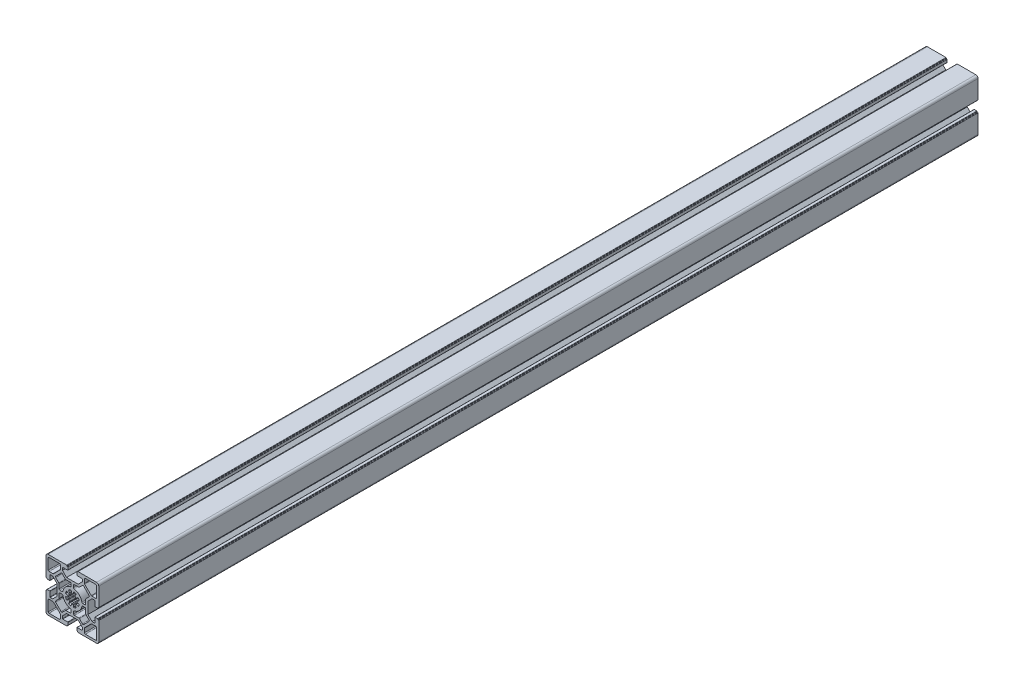
SolidWorks part; units mm, degrees
material "6063 T5"
ref_plane "Спереди" through (0, 0, 0) normal (0, 0, 1) x (1, 0, 0)
ref_plane "Сверху" through (0, 0, 0) normal (0, 1, 0) x (1, 0, 0)
ref_plane "Справа" through (0, 0, 0) normal (1, 0, 0) x (0, 0, -1)
sketch "Эскиз1" plane through (0, 0, 0) normal (0, 0, 1) x (1, 0, 0)
  line L0 (-22.505, 28.5436) -> (22.495, 28.5436) construction
  line L1 (-22.454, 23.9579) -> (22.546, 23.9579) construction
  line L73 (-30.0123, 36.8991) -> (29.9877, 36.8991) construction
  line L127 (-30, 11.25) -> (-30, 27.5)
  line L128 (-27.5, 30) -> (-11.25, 30)
  line L129 (11.25, 30) -> (27.5, 30)
  line L130 (30, 27.5) -> (30, 11.25)
  line L131 (-30, -11.25) -> (-30, -27.5)
  line L132 (-27.5, -30) -> (-11.25, -30)
  line L133 (11.25, -30) -> (27.5, -30)
  line L134 (30, -27.5) -> (30, -11.25)
  line L135 (-21.4071, 13.9929) -> (-13.9929, 21.4071)
  line L136 (-26.5, 27.5) -> (-14.7, 27.5)
  line L137 (-27.5, 26.5) -> (-27.5, 14.7)
  line L138 (-26.5, 13.7) -> (-22.1142, 13.7)
  line L139 (-13.7, 26.5) -> (-13.7, 22.1142)
  line L140 (0, 0) -> (-15.9071, 15.9071) construction
  line L141 (-12.8665, 18.9477) -> (-18.9477, 12.8665)
  line L142 (-18.9477, 11.4523) -> (-15.4929, 7.9976)
  line L143 (-15.2, 7.2905) -> (-15.2, 2.3)
  line L144 (-14.2, 1.3) -> (-11.7775, 1.3)
  line L145 (-1.3, 14.2) -> (-1.3, 11.7775)
  line L146 (-7.2905, 15.2) -> (-2.3, 15.2)
  line L147 (-11.4523, 18.9477) -> (-7.9976, 15.4929)
  line L148 (15.2, 7.2905) -> (15.2, 2.3)
  line L149 (14.2, 1.3) -> (11.7775, 1.3)
  line L150 (1.3, 14.2) -> (1.3, 11.7775)
  line L151 (7.2905, 15.2) -> (2.3, 15.2)
  line L152 (11.4523, 18.9477) -> (7.9976, 15.4929)
  line L153 (18.9477, 12.8665) -> (12.8665, 18.9477)
  line L154 (18.9477, 11.4523) -> (15.4929, 7.9976)
  line L155 (7.2905, -15.2) -> (2.3, -15.2)
  line L156 (1.3, -14.2) -> (1.3, -11.7775)
  line L157 (14.2, -1.3) -> (11.7775, -1.3)
  line L158 (15.2, -7.2905) -> (15.2, -2.3)
  line L159 (18.9477, -11.4523) -> (15.4929, -7.9976)
  line L160 (12.8665, -18.9477) -> (18.9477, -12.8665)
  line L161 (11.4523, -18.9477) -> (7.9976, -15.4929)
  line L162 (-15.2, -7.2905) -> (-15.2, -2.3)
  line L163 (-14.2, -1.3) -> (-11.7775, -1.3)
  line L164 (-1.3, -14.2) -> (-1.3, -11.7775)
  line L165 (-7.2905, -15.2) -> (-2.3, -15.2)
  line L166 (-11.4523, -18.9477) -> (-7.9976, -15.4929)
  line L167 (-18.9477, -12.8665) -> (-12.8665, -18.9477)
  line L168 (-18.9477, -11.4523) -> (-15.4929, -7.9976)
  line L169 (26.5, 13.7) -> (22.1142, 13.7)
  line L170 (13.9929, 21.4071) -> (21.4071, 13.9929)
  line L171 (13.7, 26.5) -> (13.7, 22.1142)
  line L172 (26.5, 27.5) -> (14.7, 27.5)
  line L173 (27.5, 26.5) -> (27.5, 14.7)
  line L174 (13.7, -26.5) -> (13.7, -22.1142)
  line L175 (21.4071, -13.9929) -> (13.9929, -21.4071)
  line L176 (26.5, -13.7) -> (22.1142, -13.7)
  line L177 (27.5, -26.5) -> (27.5, -14.7)
  line L178 (26.5, -27.5) -> (14.7, -27.5)
  line L179 (-26.5, -13.7) -> (-22.1142, -13.7)
  line L180 (-13.9929, -21.4071) -> (-21.4071, -13.9929)
  line L181 (-13.7, -26.5) -> (-13.7, -22.1142)
  line L182 (-26.5, -27.5) -> (-14.7, -27.5)
  line L183 (-27.5, -26.5) -> (-27.5, -14.7)
  arc A78 (-30, -27.5) -> (-27.5, -30) centre (-27.5, -27.5) ccw
  arc A79 (27.5, -30) -> (30, -27.5) centre (27.5, -27.5) ccw
  arc A80 (27.5, 30) -> (30, 27.5) centre (27.5, 27.5) cw
  arc A81 (-30, 27.5) -> (-27.5, 30) centre (-27.5, 27.5) cw
  arc A82 (-10.7961, 2.1083) -> (-2.1083, 10.7961) centre (0, 0) cw
  arc A83 (-11.7775, 1.3) -> (-10.7961, 2.1083) centre (-11.7775, 2.3) ccw
  arc A84 (-15.2, 2.3) -> (-14.2, 1.3) centre (-14.2, 2.3) ccw
  arc A85 (-15.4929, 7.9976) -> (-15.2, 7.2905) centre (-16.2, 7.2905) cw
  arc A86 (-18.9477, 12.8665) -> (-18.9477, 11.4523) centre (-18.2406, 12.1594) ccw
  arc A87 (-1.3, 11.7775) -> (-2.1083, 10.7961) centre (-2.3, 11.7775) cw
  arc A88 (-2.3, 15.2) -> (-1.3, 14.2) centre (-2.3, 14.2) cw
  arc A89 (-7.9976, 15.4929) -> (-7.2905, 15.2) centre (-7.2905, 16.2) ccw
  arc A90 (-12.8665, 18.9477) -> (-11.4523, 18.9477) centre (-12.1594, 18.2406) cw
  arc A91 (15.2, 2.3) -> (14.2, 1.3) centre (14.2, 2.3) cw
  arc A92 (11.7775, 1.3) -> (10.7961, 2.1083) centre (11.7775, 2.3) cw
  arc A93 (2.1083, 10.7961) -> (10.7961, 2.1083) centre (0, 0) cw
  arc A94 (1.3, 11.7775) -> (2.1083, 10.7961) centre (2.3, 11.7775) ccw
  arc A95 (2.3, 15.2) -> (1.3, 14.2) centre (2.3, 14.2) ccw
  arc A96 (7.9976, 15.4929) -> (7.2905, 15.2) centre (7.2905, 16.2) cw
  arc A97 (12.8665, 18.9477) -> (11.4523, 18.9477) centre (12.1594, 18.2406) ccw
  arc A98 (18.9477, 12.8665) -> (18.9477, 11.4523) centre (18.2406, 12.1594) cw
  arc A99 (15.4929, 7.9976) -> (15.2, 7.2905) centre (16.2, 7.2905) ccw
  arc A100 (2.3, -15.2) -> (1.3, -14.2) centre (2.3, -14.2) cw
  arc A101 (1.3, -11.7775) -> (2.1083, -10.7961) centre (2.3, -11.7775) cw
  arc A102 (10.7961, -2.1083) -> (2.1083, -10.7961) centre (0, 0) cw
  arc A103 (11.7775, -1.3) -> (10.7961, -2.1083) centre (11.7775, -2.3) ccw
  arc A104 (15.2, -2.3) -> (14.2, -1.3) centre (14.2, -2.3) ccw
  arc A105 (15.4929, -7.9976) -> (15.2, -7.2905) centre (16.2, -7.2905) cw
  arc A106 (18.9477, -12.8665) -> (18.9477, -11.4523) centre (18.2406, -12.1594) ccw
  arc A107 (12.8665, -18.9477) -> (11.4523, -18.9477) centre (12.1594, -18.2406) cw
  arc A108 (7.9976, -15.4929) -> (7.2905, -15.2) centre (7.2905, -16.2) ccw
  arc A109 (-15.2, -2.3) -> (-14.2, -1.3) centre (-14.2, -2.3) cw
  arc A110 (-11.7775, -1.3) -> (-10.7961, -2.1083) centre (-11.7775, -2.3) cw
  arc A111 (-2.1083, -10.7961) -> (-10.7961, -2.1083) centre (0, 0) cw
  arc A112 (-1.3, -11.7775) -> (-2.1083, -10.7961) centre (-2.3, -11.7775) ccw
  arc A113 (-2.3, -15.2) -> (-1.3, -14.2) centre (-2.3, -14.2) ccw
  arc A114 (-7.9976, -15.4929) -> (-7.2905, -15.2) centre (-7.2905, -16.2) cw
  arc A115 (-12.8665, -18.9477) -> (-11.4523, -18.9477) centre (-12.1594, -18.2406) ccw
  arc A116 (-18.9477, -12.8665) -> (-18.9477, -11.4523) centre (-18.2406, -12.1594) cw
  arc A117 (-15.4929, -7.9976) -> (-15.2, -7.2905) centre (-16.2, -7.2905) ccw
  arc A118 (-21.4071, 13.9929) -> (-22.1142, 13.7) centre (-22.1142, 14.7) cw
  arc A119 (-27.5, 14.7) -> (-26.5, 13.7) centre (-26.5, 14.7) ccw
  arc A120 (-13.9929, 21.4071) -> (-13.7, 22.1142) centre (-14.7, 22.1142) ccw
  arc A121 (-14.7, 27.5) -> (-13.7, 26.5) centre (-14.7, 26.5) cw
  arc A122 (-26.5, 27.5) -> (-27.5, 26.5) centre (-26.5, 26.5) ccw
  arc A123 (21.4071, 13.9929) -> (22.1142, 13.7) centre (22.1142, 14.7) ccw
  arc A124 (13.9929, 21.4071) -> (13.7, 22.1142) centre (14.7, 22.1142) cw
  arc A125 (14.7, 27.5) -> (13.7, 26.5) centre (14.7, 26.5) ccw
  arc A126 (27.5, 26.5) -> (26.5, 27.5) centre (26.5, 26.5) ccw
  arc A127 (27.5, 14.7) -> (26.5, 13.7) centre (26.5, 14.7) cw
  arc A128 (13.9929, -21.4071) -> (13.7, -22.1142) centre (14.7, -22.1142) ccw
  arc A129 (21.4071, -13.9929) -> (22.1142, -13.7) centre (22.1142, -14.7) cw
  arc A130 (27.5, -14.7) -> (26.5, -13.7) centre (26.5, -14.7) ccw
  arc A131 (26.5, -27.5) -> (27.5, -26.5) centre (26.5, -26.5) ccw
  arc A132 (14.7, -27.5) -> (13.7, -26.5) centre (14.7, -26.5) cw
  arc A133 (-21.4071, -13.9929) -> (-22.1142, -13.7) centre (-22.1142, -14.7) ccw
  arc A134 (-13.9929, -21.4071) -> (-13.7, -22.1142) centre (-14.7, -22.1142) cw
  arc A135 (-14.7, -27.5) -> (-13.7, -26.5) centre (-14.7, -26.5) ccw
  arc A136 (-27.5, -26.5) -> (-26.5, -27.5) centre (-26.5, -26.5) ccw
  arc A137 (-27.5, -14.7) -> (-26.5, -13.7) centre (-26.5, -14.7) cw
  point P3 (0, 0)
  point P6 (0, 0)
  point P28 (-15.2, 7.7047)
  point P31 (-19.6548, 12.1594)
  point P45 (-21.7, 13.7)
  point P60 (0, 0)
  point P121 (0, 0)
  point P124 (-27.5, 13.7)
  point P179 (0, 0)
  point P237 (0, 0)
  line B0 (-17.7, 0) -> (-30, 0) construction
  line B1 (-30, -6.1) -> (-30, 6.1) construction
  line B2 (-29.7, 6.1) -> (-29.3, 6.1)
  line B3 (-29, 5.8) -> (-29, 5.4)
  line B4 (-28.7, 5.1) -> (-25.8, 5.1)
  line B5 (-25.5, 5.4) -> (-25.5, 10.95)
  line B6 (-25.2, 11.25) -> (-22.35, 11.25)
  line B7 (-22.35, 11.25) -> (-17.7, 6.6)
  line B8 (-22.35, -11.25) -> (-17.7, -6.6)
  line B9 (-25.2, -11.25) -> (-22.35, -11.25)
  line B10 (-25.5, -5.4) -> (-25.5, -10.95)
  line B11 (-28.7, -5.1) -> (-25.8, -5.1)
  line B12 (-29, -5.8) -> (-29, -5.4)
  line B13 (-29.7, -6.1) -> (-29.3, -6.1)
  line B14 (-17.7, 6.6) -> (-17.7, -6.6)
  line B15 (-30, 6.4) -> (-30, 11.25)
  line B16 (-30, -6.4) -> (-30, -11.25)
  arc B17 (-25.2, -11.25) -> (-25.5, -10.95) centre (-25.2, -10.95) cw
  arc B18 (-25.5, -5.4) -> (-25.8, -5.1) centre (-25.8, -5.4) ccw
  arc B19 (-28.7, -5.1) -> (-29, -5.4) centre (-28.7, -5.4) ccw
  arc B20 (-29, -5.8) -> (-29.3, -6.1) centre (-29.3, -5.8) cw
  arc B21 (-29.7, -6.1) -> (-30, -6.4) centre (-29.7, -6.4) ccw
  arc B22 (-25.5, 10.95) -> (-25.2, 11.25) centre (-25.2, 10.95) cw
  arc B23 (-25.8, 5.1) -> (-25.5, 5.4) centre (-25.8, 5.4) ccw
  arc B24 (-29, 5.4) -> (-28.7, 5.1) centre (-28.7, 5.4) ccw
  arc B25 (-29.3, 6.1) -> (-29, 5.8) centre (-29.3, 5.8) cw
  arc B26 (-29.7, 6.1) -> (-30, 6.4) centre (-29.7, 6.4) cw
  line B27 (0, 17.7) -> (0, 30) construction
  line B28 (-6.1, 30) -> (6.1, 30) construction
  line B29 (6.1, 29.7) -> (6.1, 29.3)
  line B30 (5.8, 29) -> (5.4, 29)
  line B31 (5.1, 28.7) -> (5.1, 25.8)
  line B32 (5.4, 25.5) -> (10.95, 25.5)
  line B33 (11.25, 25.2) -> (11.25, 22.35)
  line B34 (11.25, 22.35) -> (6.6, 17.7)
  line B35 (-11.25, 22.35) -> (-6.6, 17.7)
  line B36 (-11.25, 25.2) -> (-11.25, 22.35)
  line B37 (-5.4, 25.5) -> (-10.95, 25.5)
  line B38 (-5.1, 28.7) -> (-5.1, 25.8)
  line B39 (-5.8, 29) -> (-5.4, 29)
  line B40 (-6.1, 29.7) -> (-6.1, 29.3)
  line B41 (6.6, 17.7) -> (-6.6, 17.7)
  line B42 (6.4, 30) -> (11.25, 30)
  line B43 (-6.4, 30) -> (-11.25, 30)
  arc B44 (-11.25, 25.2) -> (-10.95, 25.5) centre (-10.95, 25.2) cw
  arc B45 (-5.4, 25.5) -> (-5.1, 25.8) centre (-5.4, 25.8) ccw
  arc B46 (-5.1, 28.7) -> (-5.4, 29) centre (-5.4, 28.7) ccw
  arc B47 (-5.8, 29) -> (-6.1, 29.3) centre (-5.8, 29.3) cw
  arc B48 (-6.1, 29.7) -> (-6.4, 30) centre (-6.4, 29.7) ccw
  arc B49 (10.95, 25.5) -> (11.25, 25.2) centre (10.95, 25.2) cw
  arc B50 (5.1, 25.8) -> (5.4, 25.5) centre (5.4, 25.8) ccw
  arc B51 (5.4, 29) -> (5.1, 28.7) centre (5.4, 28.7) ccw
  arc B52 (6.1, 29.3) -> (5.8, 29) centre (5.8, 29.3) cw
  arc B53 (6.1, 29.7) -> (6.4, 30) centre (6.4, 29.7) cw
  line B54 (17.7, 0) -> (30, 0) construction
  line B55 (30, 6.1) -> (30, -6.1) construction
  line B56 (29.7, -6.1) -> (29.3, -6.1)
  line B57 (29, -5.8) -> (29, -5.4)
  line B58 (28.7, -5.1) -> (25.8, -5.1)
  line B59 (25.5, -5.4) -> (25.5, -10.95)
  line B60 (25.2, -11.25) -> (22.35, -11.25)
  line B61 (22.35, -11.25) -> (17.7, -6.6)
  line B62 (22.35, 11.25) -> (17.7, 6.6)
  line B63 (25.2, 11.25) -> (22.35, 11.25)
  line B64 (25.5, 5.4) -> (25.5, 10.95)
  line B65 (28.7, 5.1) -> (25.8, 5.1)
  line B66 (29, 5.8) -> (29, 5.4)
  line B67 (29.7, 6.1) -> (29.3, 6.1)
  line B68 (17.7, -6.6) -> (17.7, 6.6)
  line B69 (30, -6.4) -> (30, -11.25)
  line B70 (30, 6.4) -> (30, 11.25)
  arc B71 (25.2, 11.25) -> (25.5, 10.95) centre (25.2, 10.95) cw
  arc B72 (25.5, 5.4) -> (25.8, 5.1) centre (25.8, 5.4) ccw
  arc B73 (28.7, 5.1) -> (29, 5.4) centre (28.7, 5.4) ccw
  arc B74 (29, 5.8) -> (29.3, 6.1) centre (29.3, 5.8) cw
  arc B75 (29.7, 6.1) -> (30, 6.4) centre (29.7, 6.4) ccw
  arc B76 (25.5, -10.95) -> (25.2, -11.25) centre (25.2, -10.95) cw
  arc B77 (25.8, -5.1) -> (25.5, -5.4) centre (25.8, -5.4) ccw
  arc B78 (29, -5.4) -> (28.7, -5.1) centre (28.7, -5.4) ccw
  arc B79 (29.3, -6.1) -> (29, -5.8) centre (29.3, -5.8) cw
  arc B80 (29.7, -6.1) -> (30, -6.4) centre (29.7, -6.4) cw
  line B81 (0, -17.7) -> (0, -30) construction
  line B82 (6.1, -30) -> (-6.1, -30) construction
  line B83 (-6.1, -29.7) -> (-6.1, -29.3)
  line B84 (-5.8, -29) -> (-5.4, -29)
  line B85 (-5.1, -28.7) -> (-5.1, -25.8)
  line B86 (-5.4, -25.5) -> (-10.95, -25.5)
  line B87 (-11.25, -25.2) -> (-11.25, -22.35)
  line B88 (-11.25, -22.35) -> (-6.6, -17.7)
  line B89 (11.25, -22.35) -> (6.6, -17.7)
  line B90 (11.25, -25.2) -> (11.25, -22.35)
  line B91 (5.4, -25.5) -> (10.95, -25.5)
  line B92 (5.1, -28.7) -> (5.1, -25.8)
  line B93 (5.8, -29) -> (5.4, -29)
  line B94 (6.1, -29.7) -> (6.1, -29.3)
  line B95 (-6.6, -17.7) -> (6.6, -17.7)
  line B96 (-6.4, -30) -> (-11.25, -30)
  line B97 (6.4, -30) -> (11.25, -30)
  arc B98 (11.25, -25.2) -> (10.95, -25.5) centre (10.95, -25.2) cw
  arc B99 (5.4, -25.5) -> (5.1, -25.8) centre (5.4, -25.8) ccw
  arc B100 (5.1, -28.7) -> (5.4, -29) centre (5.4, -28.7) ccw
  arc B101 (5.8, -29) -> (6.1, -29.3) centre (5.8, -29.3) cw
  arc B102 (6.1, -29.7) -> (6.4, -30) centre (6.4, -29.7) ccw
  arc B103 (-10.95, -25.5) -> (-11.25, -25.2) centre (-10.95, -25.2) cw
  arc B104 (-5.1, -25.8) -> (-5.4, -25.5) centre (-5.4, -25.8) ccw
  arc B105 (-5.4, -29) -> (-5.1, -28.7) centre (-5.4, -28.7) ccw
  arc B106 (-6.1, -29.3) -> (-5.8, -29) centre (-5.8, -29.3) cw
  arc B107 (-6.1, -29.7) -> (-6.4, -30) centre (-6.4, -29.7) cw
  line B108 (0, 0) -> (3.6062, 3.6062) construction
  line B109 (1.3637, 7.358) -> (1.0164, 5.4842)
  line B110 (3.1592, 4.5967) -> (4.2386, 6.1672)
  line B111 (0, 0) -> (0, 5.1) construction
  arc B112 (0.478, -5.0776) -> (-0.478, -5.0776) centre (0, 0) cw
  arc B113 (-6.8804, -4.0816) -> (-7.7513, -1.979) centre (0, 0) cw
  arc B114 (3.9283, 3.2524) -> (3.2524, 3.9283) centre (0, 0) ccw
  arc B115 (4.0816, 6.8804) -> (1.979, 7.7513) centre (0, 0) ccw
  arc B116 (0.478, 5.0776) -> (-0.478, 5.0776) centre (0, 0) ccw
  line B117 (-1.3637, 7.358) -> (-1.0164, 5.4842)
  arc B118 (4.0816, -6.8804) -> (1.979, -7.7513) centre (0, 0) cw
  arc B119 (-3.9283, -3.2524) -> (-3.2524, -3.9283) centre (0, 0) ccw
  line B120 (-3.1592, -4.5967) -> (-4.2386, -6.1672)
  line B121 (0, 0) -> (6.3318, 0) construction
  line B122 (4.5967, 3.1592) -> (6.1672, 4.2386)
  line B123 (7.358, 1.3637) -> (5.4842, 1.0164)
  line B124 (-7.358, 1.3637) -> (-5.4842, 1.0164)
  line B125 (-4.5967, 3.1592) -> (-6.1672, 4.2386)
  line B126 (-3.1592, 4.5967) -> (-4.2386, 6.1672)
  line B127 (7.358, -1.3637) -> (5.4842, -1.0164)
  line B128 (4.5967, -3.1592) -> (6.1672, -4.2386)
  line B129 (3.1592, -4.5967) -> (4.2386, -6.1672)
  line B130 (1.3637, -7.358) -> (1.0164, -5.4842)
  line B131 (-1.3637, -7.358) -> (-1.0164, -5.4842)
  line B132 (-4.5967, -3.1592) -> (-6.1672, -4.2386)
  line B133 (-7.358, -1.3637) -> (-5.4842, -1.0164)
  arc B134 (5.0776, 0.478) -> (5.0776, -0.478) centre (0, 0) cw
  arc B135 (6.8804, 4.0816) -> (7.7513, 1.979) centre (0, 0) cw
  arc B136 (-5.0776, 0.478) -> (-5.0776, -0.478) centre (0, 0) ccw
  arc B137 (-6.8804, 4.0816) -> (-7.7513, 1.979) centre (0, 0) ccw
  arc B138 (-3.9283, 3.2524) -> (-3.2524, 3.9283) centre (0, 0) cw
  arc B139 (-4.0816, 6.8804) -> (-1.979, 7.7513) centre (0, 0) cw
  arc B140 (6.8804, -4.0816) -> (7.7513, -1.979) centre (0, 0) ccw
  arc B141 (3.9283, -3.2524) -> (3.2524, -3.9283) centre (0, 0) cw
  arc B142 (-4.0816, -6.8804) -> (-1.979, -7.7513) centre (0, 0) ccw
  arc B143 (-1.979, 7.7513) -> (-1.3637, 7.358) centre (-1.8554, 7.2669) cw
  arc B144 (-4.0816, 6.8804) -> (-4.2386, 6.1672) centre (-3.8265, 6.4504) ccw
  arc B145 (-3.2524, 3.9283) -> (-3.1592, 4.5967) centre (-3.5713, 4.3135) ccw
  arc B146 (-3.9283, 3.2524) -> (-4.5967, 3.1592) centre (-4.3135, 3.5713) cw
  arc B147 (-6.8804, 4.0816) -> (-6.1672, 4.2386) centre (-6.4504, 3.8265) cw
  arc B148 (-7.7513, 1.979) -> (-7.358, 1.3637) centre (-7.2669, 1.8554) ccw
  arc B149 (-5.0776, 0.478) -> (-5.4842, 1.0164) centre (-5.5754, 0.5248) ccw
  arc B150 (-5.4842, -1.0164) -> (-5.0776, -0.478) centre (-5.5754, -0.5248) ccw
  arc B151 (-7.7513, -1.979) -> (-7.358, -1.3637) centre (-7.2669, -1.8554) cw
  arc B152 (-6.8804, -4.0816) -> (-6.1672, -4.2386) centre (-6.4504, -3.8265) ccw
  arc B153 (-3.9283, -3.2524) -> (-4.5967, -3.1592) centre (-4.3135, -3.5713) ccw
  arc B154 (-3.2524, -3.9283) -> (-3.1592, -4.5967) centre (-3.5713, -4.3135) cw
  arc B155 (-4.0816, -6.8804) -> (-4.2386, -6.1672) centre (-3.8265, -6.4504) cw
  arc B156 (-1.979, -7.7513) -> (-1.3637, -7.358) centre (-1.8554, -7.2669) ccw
  arc B157 (-0.478, -5.0776) -> (-1.0164, -5.4842) centre (-0.5248, -5.5754) ccw
  arc B158 (0.478, -5.0776) -> (1.0164, -5.4842) centre (0.5248, -5.5754) cw
  arc B159 (1.979, -7.7513) -> (1.3637, -7.358) centre (1.8554, -7.2669) cw
  arc B160 (4.0816, -6.8804) -> (4.2386, -6.1672) centre (3.8265, -6.4504) ccw
  arc B161 (3.2524, -3.9283) -> (3.1592, -4.5967) centre (3.5713, -4.3135) ccw
  arc B162 (3.9283, -3.2524) -> (4.5967, -3.1592) centre (4.3135, -3.5713) cw
  arc B163 (6.8804, -4.0816) -> (6.1672, -4.2386) centre (6.4504, -3.8265) cw
  arc B164 (7.7513, -1.979) -> (7.358, -1.3637) centre (7.2669, -1.8554) ccw
  arc B165 (5.4842, -1.0164) -> (5.0776, -0.478) centre (5.5754, -0.5248) cw
  arc B166 (5.0776, 0.478) -> (5.4842, 1.0164) centre (5.5754, 0.5248) cw
  arc B167 (7.7513, 1.979) -> (7.358, 1.3637) centre (7.2669, 1.8554) cw
  arc B168 (6.8804, 4.0816) -> (6.1672, 4.2386) centre (6.4504, 3.8265) ccw
  arc B169 (4.5967, 3.1592) -> (3.9283, 3.2524) centre (4.3135, 3.5713) cw
  arc B170 (3.1592, 4.5967) -> (3.2524, 3.9283) centre (3.5713, 4.3135) ccw
  arc B171 (4.2386, 6.1672) -> (4.0816, 6.8804) centre (3.8265, 6.4504) ccw
  arc B172 (1.3637, 7.358) -> (1.979, 7.7513) centre (1.8554, 7.2669) cw
  arc B173 (-1.0164, 5.4842) -> (-0.478, 5.0776) centre (-0.5248, 5.5754) ccw
  arc B174 (1.0164, 5.4842) -> (0.478, 5.0776) centre (0.5248, 5.5754) cw
  dimension "D5" = 60
  dimension "D3" = 4
  dimension "D11" = 45
  dimension "D6" = 13.8
  dimension "D7" = 2.5
  dimension "D20" = 4
  dimension "D23" = 2.5
  dimension "D15" = 11
  dimension "D17" = 1
  dimension "D19" = 1
  dimension "D1" = 45
  dimension "D2" = 30
  dimension "D4" = 45
  dimension "D8" = 5.8
  dimension "D9" = 2.5
  dimension "D10" = 135
  dimension "D12" = 5.3
  dimension "D13" = 2.5
  dimension "D14" = 6.3
  dimension "D16" = 1.3
  dimension "D18" = 4
sketch_block_instance "Блок1-1"
sketch_block "Блок1" parameters "D4"=8.1, "D10"=0.3, "D1"=22.5, "D2"=45, "D3"=0.7, "D5"=1, "D6"=10.2, "D7"=22.5, "D8"=4.5, "D9"=12.2, "D11"=1.2, "D12"=3.2
sketch_block_instance "Блок1-7"
sketch_block_instance "Блок1-8"
sketch_block_instance "Блок1-9"
sketch_block_instance "star_R5,1_R8-1"
sketch_block "star_R5,1_R8" parameters "D1"=10.2, "D5"=16, "D6"=0.5, "D2"=10.5, "D3"=24, "D4"=45
extrude "Бобышка-Вытянуть1" add sketch "Эскиз1" along normal blind 1000
